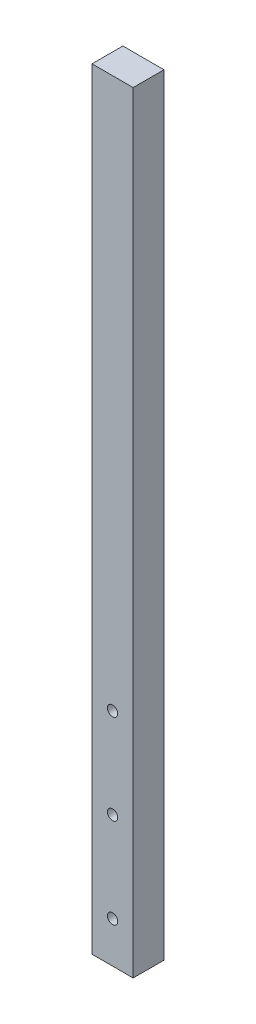
SolidWorks part; units mm, degrees
ref_plane "Front Plane" through (0, 0, 0) normal (0, 0, 1) x (1, 0, 0)
ref_plane "Top Plane" through (0, 0, 0) normal (0, 1, 0) x (1, 0, 0)
ref_plane "Right Plane" through (0, 0, 0) normal (1, 0, 0) x (0, 0, -1)
sketch "Model" plane through (0, 0, 0) normal (0, 0, 1) x (1, 0, 0)
  line L0 (47.8216, 157.0133) -> (47.8216, 7.0133)
  line L1 (47.8216, 7.0133) -> (55.8216, 7.0133)
  line L2 (55.8216, 7.0133) -> (55.8216, 157.0133)
  line L3 (55.8216, 157.0133) -> (47.8216, 157.0133)
  circle A0 centre (51.8216, 15.0133) radius 1
  circle A1 centre (51.8216, 50.0133) radius 1
  circle A2 centre (51.8216, 32.5133) radius 1
extrude "Boss-Extrude2" add sketch "Model" along normal blind 6 contours L2 L3 L0 L1 | A1 | A0 | A2
